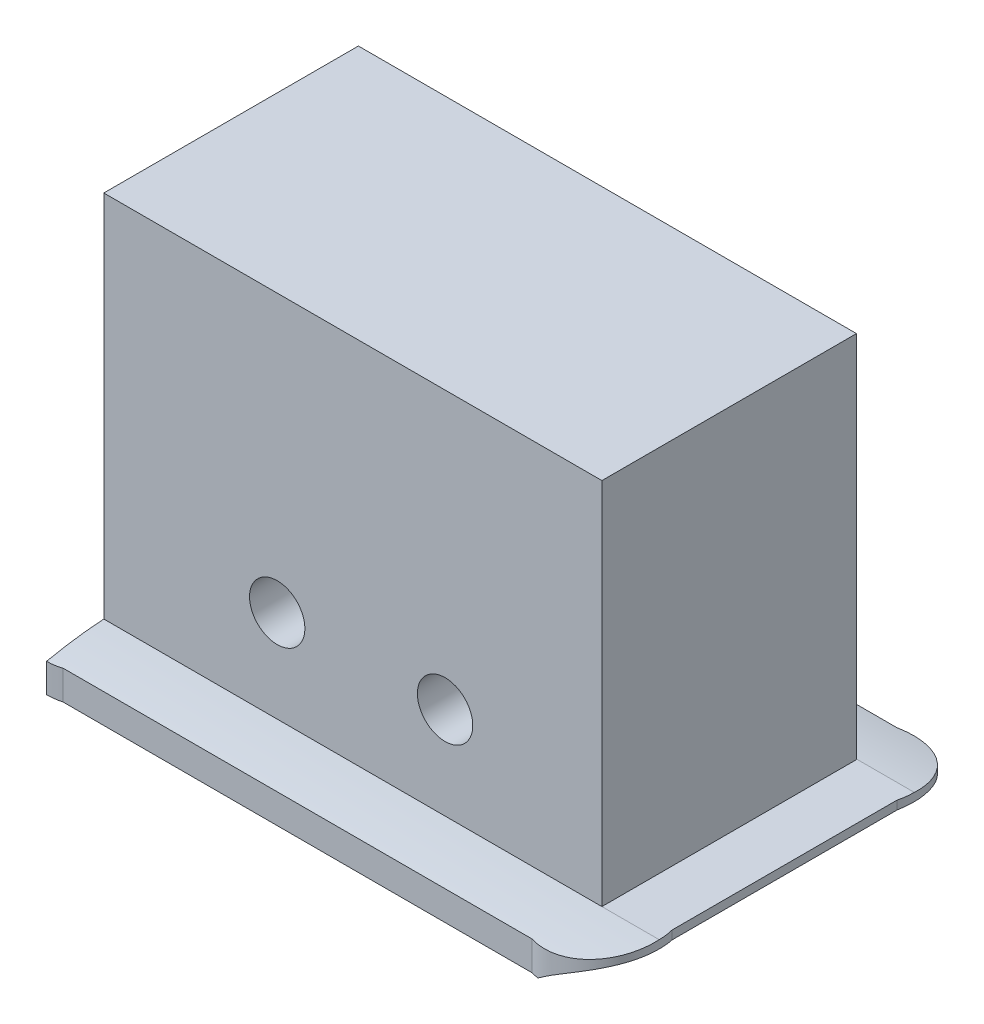
SolidWorks part; units mm, degrees
ref_plane "Front Plane" through (0, 0, 0) normal (0, 0, 1) x (1, 0, 0)
ref_plane "Top Plane" through (0, 0, 0) normal (0, 1, 0) x (1, 0, 0)
ref_plane "Right Plane" through (0, 0, 0) normal (1, 0, 0) x (0, 0, -1)
sketch "Sketch1" plane through (0, 0, 0) normal (0, 1, 0) x (1, 0, 0)
  line L0 (-3, 10.8) -> (24, 10.8)
  line L1 (0, 7.8) -> (21, 7.8)
  line L2 (0, 7.8) -> (0, 0)
  line L3 (0, 0) -> (21, 0)
  line L4 (21, 7.8) -> (21, 0)
  line L9 (24, 10.8) -> (24, -3)
  line L10 (-3, -3) -> (24, -3)
  line L11 (-3, 10.8) -> (-3, -3)
  dimension "D1" = 21
  dimension "D2" = 7.8
  dimension "D3" = 3
extrude "Boss-Extrude1" add sketch "Sketch1" along normal blind 22
sketch "Sketch3" plane through (0, 22, 0) normal (0, 1, 0) x (1, 0, 0)
  line L0 (0, 0) -> (21, 0) construction
  line L1 (21, 0) -> (21, 7.8) construction
  line L2 (21, 7.8) -> (0, 7.8) construction
  line L3 (0, 7.8) -> (0, 0) construction
  line L4 (0, 0) -> (21, 0)
  line L5 (21, 0) -> (21, 7.8)
  line L6 (21, 7.8) -> (0, 7.8)
  line L7 (0, 7.8) -> (0, 0)
extrude "Boss-Extrude2" add sketch "Sketch3" against normal blind 2
sketch "Sketch4" plane through (0, 22, 0) normal (0, 1, 0) x (1, 0, 0)
  line L1 (4.1034, 3.9) -> (4.1034, 10.8) construction
  line L2 (24, 10.8) -> (-3, 10.8) construction
  line L3 (4.1034, 3.9) -> (4.1034, -3) construction
  line L4 (-3, -3) -> (24, -3) construction
  circle A0 centre (4.1034, 3.9) radius 3
  dimension "D1" = 6
sketch "Sketch6" plane through (0, 0, 0) normal (0, -1, 0) x (1, 0, 0)
  line L4 (-3, -3.9) -> (31.2377, -3.9) construction
  line L5 (-3, -10.8) -> (-3, 3) construction
  line L6 (10.5, 3) -> (10.5, -26.2462) construction
  line L7 (-3, 3) -> (24, 3) construction
  line L8 (-6, 6) -> (-6, -13.8)
  line L9 (-6, -13.8) -> (27, -13.8)
  line L10 (27, -13.8) -> (27, 6)
  line L11 (27, 6) -> (-6, 6)
  line L12 (-6, 2.2) -> (-6, -10)
  line L13 (-2.2, -13.8) -> (23.2, -13.8)
  line L14 (27, -10) -> (27, 2.2)
  line L15 (23.2, 6) -> (-2.2, 6)
  line L16 (24, -10.8) -> (-3, -10.8) construction
  line L17 (24, 3) -> (24, -10.8) construction
  line L18 (-3, -10.8) -> (-3, 3)
  line L19 (24, -10.8) -> (-3, -10.8)
  line L20 (24, 3) -> (24, -10.8)
  line L21 (-3, 3) -> (24, 3)
  arc A0 (27, 2.2) -> (23.2, 6) centre (24, 3) ccw
  arc A1 (27, -10) -> (23.2, -13.8) centre (24, -10.8) cw
  arc A2 (-6, -10) -> (-2.2, -13.8) centre (-3, -10.8) ccw
  arc A3 (-6, 2.2) -> (-2.2, 6) centre (-3, 3) cw
  dimension "D1" = 3
extrude "Boss-Extrude3" add sketch "Sketch6" against normal blind 2
sketch "Sketch7" plane through (0, 0, -10.8) normal (0, 0, -1) x (-1, 0, 0)
  line L0 (2.2, 0) -> (-23.2, 0) construction
  line L2 (-21, 20) -> (-21, 0) construction
  circle A0 centre (-15.5, 7) radius 1.5
  circle A1 centre (-6.4, 7) radius 1.5
  dimension "D3" = 3
  dimension "D4" = 3
  dimension "D1" = 7
  dimension "D2" = 7
  dimension "D5" = 9.1
  dimension "D6" = 5.5
sketch "Sketch8" plane through (-3, 0, 0) normal (-1, 0, 0) x (0, 0, 1)
  line L0 (-3.9, 16.8165) -> (3, 16.8165) construction
  line L1 (3, 22) -> (3, 2) construction
  line L2 (-3.9, 16.8165) -> (-10.8, 16.8165) construction
  line L3 (-10.8, 22) -> (-10.8, 2) construction
  circle A0 centre (-3.9, 16.8165) radius 3
  dimension "D1" = 6
extrude "Cut-Extrude2" cut sketch "Sketch8" against normal blind 5
ref_plane "Plane3" through (27, 0, -10) normal (0, 0, 1) x (1, 0, 0)
sketch "Sketch12" plane through (-6, 0, 0) normal (-1, 0, 0) x (0, 0, 1)
  line L0 (3, 2) -> (6.1048, 2)
  line L1 (6.1048, 2) -> (6.1048, 1.5668)
  line L2 (6.1048, 0) -> (6.1048, 2) construction
  line L3 (-3.9145, 16.7797) -> (-3.9145, -4.906) construction
  line L4 (-13.9338, 2) -> (-13.9338, 1.5668)
  line L5 (-10.8289, 2) -> (-13.9338, 2)
  circle A0 centre (-3.9145, -58.1923) radius 60 construction
  spline S0 degree 2 poles (6.1048, 1.5668) (4.5709, 1.8985) (3, 2) knots 0 0 0 1 1 1
  spline S1 degree 2 poles (-13.9338, 1.5668) (-12.3999, 1.8985) (-10.8289, 2) knots 0 0 0 1 1 1
  dimension "D1" = 120
extrude "Cut-Extrude3" cut sketch "Sketch12" against normal blind 45
sketch "Sketch13" plane through (27, 0, -10) normal (0, 0, 1) x (1, 0, 0)
  line L2 (-3.3779, 0) -> (0.5096, 0)
  line L3 (0.5096, 0) -> (0.5096, 1.5757)
  line L4 (0.5096, 1.5757) -> (0.1756, 1.5757)
  spline S0 degree 3 poles (-3.3779, 0) (-2.3375, 0.8071) (-1.0904, 1.274) (0.1756, 1.5757) knots 0 0 0 0 1 1 1 1
extrude "Cut-Extrude5" cut sketch "Sketch13" against normal blind 45 and the other way blind 45
extrude "Cut-Extrude6" cut sketch "Sketch7" against normal through all both and the other way through all contours A1 | A0
sketch "Sketch15" plane through (0, 0, 3) normal (0, 0, 1) x (1, 0, 0)
  line L1 (-3, 2) -> (-7.5184, 2)
  line L2 (-3, 2) -> (-3, -2.3071)
  line L3 (-3, -2.3071) -> (-7.5184, -2.3071)
  line L4 (-7.5184, 2) -> (-7.5184, -2.3071)
extrude "Cut-Extrude7" cut sketch "Sketch15" against normal blind 20 and the other way blind 10
